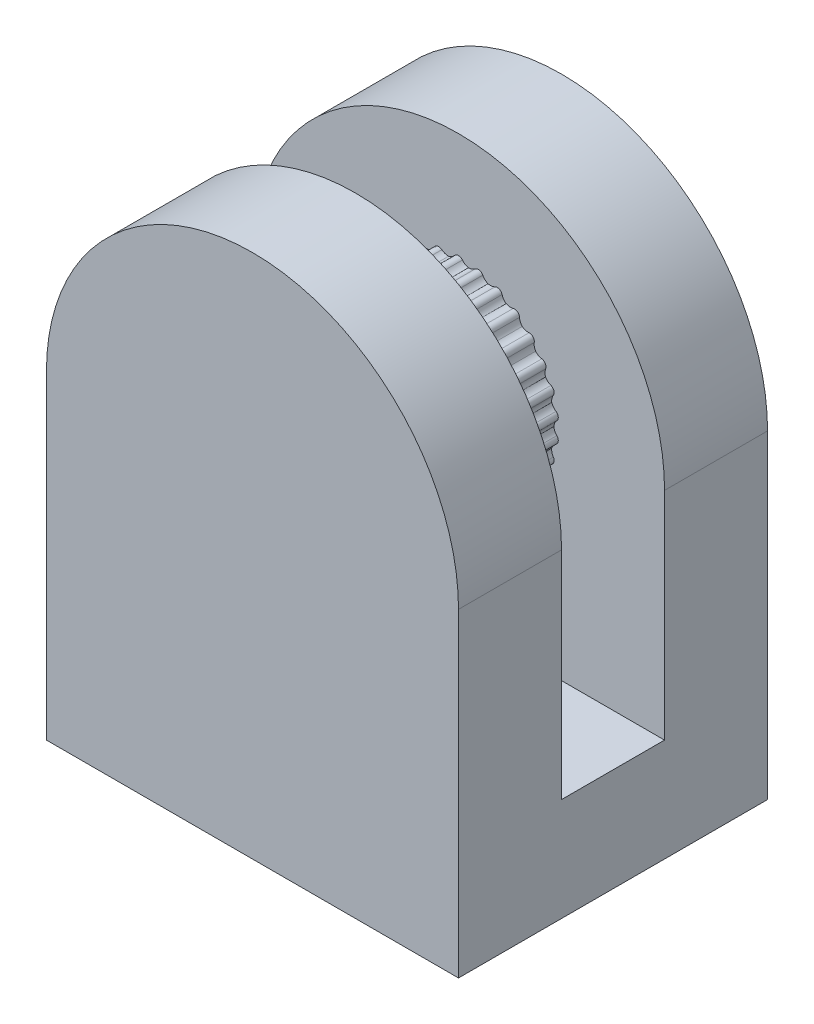
SolidWorks part; units mm, degrees
ref_plane "Front Plane" through (0, 0, 0) normal (0, 0, 1) x (1, 0, 0)
ref_plane "Top Plane" through (0, 0, 0) normal (0, 1, 0) x (1, 0, 0)
ref_plane "Right Plane" through (0, 0, 0) normal (1, 0, 0) x (0, 0, -1)
sketch "Sketch1" plane through (0, 0, 0) normal (0, 0, 1) x (1, 0, 0)
  circle A0 centre (0, 0) radius 20
  arc A1 (0.3787, 9.556) -> (-0.3787, 9.556) centre (0, 9.25) ccw
  arc A2 (2.3572, 9.2685) -> (1.6164, 9.4259) centre (1.9232, 9.0479) ccw
  arc A3 (4.2327, 8.5758) -> (3.5409, 8.8839) centre (3.7623, 8.4503) ccw
  arc A4 (5.9232, 7.5084) -> (5.3105, 7.9535) centre (5.437, 7.4834) ccw
  arc A5 (7.3549, 6.1128) -> (6.8481, 6.6756) centre (6.8741, 6.1895) ccw
  arc A6 (8.4651, 4.4501) -> (8.0864, 5.1059) centre (8.0107, 4.625) ccw
  arc A7 (9.2053, 2.5929) -> (8.9713, 3.3131) centre (8.7973, 2.8584) ccw
  arc A8 (9.5432, 0.6223) -> (9.4641, 1.3755) centre (9.1993, 0.9669) ccw
  arc A9 (9.4641, -1.3755) -> (9.5432, -0.6223) centre (9.1993, -0.9669) ccw
  arc A10 (8.9713, -3.3131) -> (9.2053, -2.5929) centre (8.7973, -2.8584) ccw
  arc A11 (8.0864, -5.1059) -> (8.4651, -4.4501) centre (8.0107, -4.625) ccw
  arc A12 (6.8481, -6.6756) -> (7.3549, -6.1128) centre (6.8741, -6.1895) ccw
  arc A13 (5.3105, -7.9535) -> (5.9232, -7.5084) centre (5.437, -7.4834) ccw
  arc A14 (3.5409, -8.8839) -> (4.2327, -8.5758) centre (3.7623, -8.4503) ccw
  arc A15 (1.6164, -9.4259) -> (2.3572, -9.2685) centre (1.9232, -9.0479) ccw
  arc A16 (-0.3787, -9.556) -> (0.3787, -9.556) centre (0, -9.25) ccw
  arc A17 (-2.3572, -9.2685) -> (-1.6164, -9.4259) centre (-1.9232, -9.0479) ccw
  arc A18 (-4.2327, -8.5758) -> (-3.5409, -8.8839) centre (-3.7623, -8.4503) ccw
  arc A19 (-5.9232, -7.5084) -> (-5.3105, -7.9535) centre (-5.437, -7.4834) ccw
  arc A20 (-7.3549, -6.1128) -> (-6.8481, -6.6756) centre (-6.8741, -6.1895) ccw
  arc A21 (-8.4651, -4.4501) -> (-8.0864, -5.1059) centre (-8.0107, -4.625) ccw
  arc A22 (-9.2053, -2.5929) -> (-8.9713, -3.3131) centre (-8.7973, -2.8584) ccw
  arc A23 (-9.5432, -0.6223) -> (-9.4641, -1.3755) centre (-9.1993, -0.9669) ccw
  arc A24 (-9.4641, 1.3755) -> (-9.5432, 0.6223) centre (-9.1993, 0.9669) ccw
  arc A25 (-8.9713, 3.3131) -> (-9.2053, 2.5929) centre (-8.7973, 2.8584) ccw
  arc A26 (-8.0864, 5.1059) -> (-8.4651, 4.4501) centre (-8.0107, 4.625) ccw
  arc A27 (-6.8481, 6.6756) -> (-7.3549, 6.1128) centre (-6.8741, 6.1895) ccw
  arc A28 (-5.3105, 7.9535) -> (-5.9232, 7.5084) centre (-5.437, 7.4834) ccw
  arc A29 (-3.5409, 8.8839) -> (-4.2327, 8.5758) centre (-3.7623, 8.4503) ccw
  arc A30 (-1.6164, 9.4259) -> (-2.3572, 9.2685) centre (-1.9232, 9.0479) ccw
  arc A31 (-0.3787, 9.556) -> (-0.9672, 9.2026) centre (-1.1564, 10.1846) cw
  arc A32 (0.9672, 9.2026) -> (0.3787, 9.556) centre (1.1564, 10.1846) cw
  arc A33 (1.6164, 9.4259) -> (0.9672, 9.2026) centre (0.9863, 10.2024) cw
  arc A34 (2.8594, 8.8004) -> (2.3572, 9.2685) centre (3.2486, 9.7216) cw
  arc A35 (3.5409, 8.8839) -> (2.8594, 8.8004) centre (3.086, 9.7744) cw
  arc A36 (4.6267, 8.0136) -> (4.2327, 8.5758) centre (5.1989, 8.8337) cw
  arc A37 (5.3105, 7.9535) -> (4.6267, 8.0136) centre (5.0508, 8.9192) cw
  arc A38 (6.1917, 6.8765) -> (5.9232, 7.5084) centre (6.9219, 7.5598) cw
  arc A39 (6.8481, 6.6756) -> (6.1917, 6.8765) centre (6.7948, 7.6742) cw
  arc A40 (7.4861, 5.439) -> (7.3549, 6.1128) centre (8.3424, 5.9554) cw
  arc A41 (8.0864, 5.1059) -> (7.4861, 5.439) centre (8.2419, 6.0938) cw
  arc A42 (8.4533, 3.7637) -> (8.4651, 4.4501) centre (9.3983, 4.0908) cw
  arc A43 (8.9713, 3.3131) -> (8.4533, 3.7637) centre (9.3287, 4.247) cw
  arc A44 (9.0511, 1.9239) -> (9.2053, 2.5929) centre (10.0434, 2.0474) cw
  arc A45 (9.4641, 1.3755) -> (9.0511, 1.9239) centre (10.0079, 2.2147) cw
  arc A46 (9.2533, 0) -> (9.5432, 0.6223) centre (10.2496, -0.0855) cw
  arc A47 (9.5432, -0.6223) -> (9.2533, 0) centre (10.2496, 0.0855) cw
  arc A48 (9.0511, -1.9239) -> (9.4641, -1.3755) centre (10.0079, -2.2147) cw
  arc A49 (9.2053, -2.5929) -> (9.0511, -1.9239) centre (10.0434, -2.0474) cw
  arc A50 (8.4533, -3.7637) -> (8.9713, -3.3131) centre (9.3287, -4.247) cw
  arc A51 (8.4651, -4.4501) -> (8.4533, -3.7637) centre (9.3983, -4.0908) cw
  arc A52 (7.4861, -5.439) -> (8.0864, -5.1059) centre (8.2419, -6.0938) cw
  arc A53 (7.3549, -6.1128) -> (7.4861, -5.439) centre (8.3424, -5.9554) cw
  arc A54 (6.1917, -6.8765) -> (6.8481, -6.6756) centre (6.7948, -7.6742) cw
  arc A55 (5.9232, -7.5084) -> (6.1917, -6.8765) centre (6.9219, -7.5598) cw
  arc A56 (4.6267, -8.0136) -> (5.3105, -7.9535) centre (5.0508, -8.9192) cw
  arc A57 (4.2327, -8.5758) -> (4.6267, -8.0136) centre (5.1989, -8.8337) cw
  arc A58 (2.8594, -8.8004) -> (3.5409, -8.8839) centre (3.086, -9.7744) cw
  arc A59 (2.3572, -9.2685) -> (2.8594, -8.8004) centre (3.2486, -9.7216) cw
  arc A60 (0.9672, -9.2026) -> (1.6164, -9.4259) centre (0.9863, -10.2024) cw
  arc A61 (0.3787, -9.556) -> (0.9672, -9.2026) centre (1.1564, -10.1846) cw
  arc A62 (-0.9672, -9.2026) -> (-0.3787, -9.556) centre (-1.1564, -10.1846) cw
  arc A63 (-1.6164, -9.4259) -> (-0.9672, -9.2026) centre (-0.9863, -10.2024) cw
  arc A64 (-2.8594, -8.8004) -> (-2.3572, -9.2685) centre (-3.2486, -9.7216) cw
  arc A65 (-3.5409, -8.8839) -> (-2.8594, -8.8004) centre (-3.086, -9.7744) cw
  arc A66 (-4.6267, -8.0136) -> (-4.2327, -8.5758) centre (-5.1989, -8.8337) cw
  arc A67 (-5.3105, -7.9535) -> (-4.6267, -8.0136) centre (-5.0508, -8.9192) cw
  arc A68 (-6.1917, -6.8765) -> (-5.9232, -7.5084) centre (-6.9219, -7.5598) cw
  arc A69 (-6.8481, -6.6756) -> (-6.1917, -6.8765) centre (-6.7948, -7.6742) cw
  arc A70 (-7.4861, -5.439) -> (-7.3549, -6.1128) centre (-8.3424, -5.9554) cw
  arc A71 (-8.0864, -5.1059) -> (-7.4861, -5.439) centre (-8.2419, -6.0938) cw
  arc A72 (-8.4533, -3.7637) -> (-8.4651, -4.4501) centre (-9.3983, -4.0908) cw
  arc A73 (-8.9713, -3.3131) -> (-8.4533, -3.7637) centre (-9.3287, -4.247) cw
  arc A74 (-9.0511, -1.9239) -> (-9.2053, -2.5929) centre (-10.0434, -2.0474) cw
  arc A75 (-9.4641, -1.3755) -> (-9.0511, -1.9239) centre (-10.0079, -2.2147) cw
  arc A76 (-9.2533, 0) -> (-9.5432, -0.6223) centre (-10.2496, 0.0855) cw
  arc A77 (-9.5432, 0.6223) -> (-9.2533, 0) centre (-10.2496, -0.0855) cw
  arc A78 (-9.0511, 1.9239) -> (-9.4641, 1.3755) centre (-10.0079, 2.2147) cw
  arc A79 (-9.2053, 2.5929) -> (-9.0511, 1.9239) centre (-10.0434, 2.0474) cw
  arc A80 (-8.4533, 3.7637) -> (-8.9713, 3.3131) centre (-9.3287, 4.247) cw
  arc A81 (-8.4651, 4.4501) -> (-8.4533, 3.7637) centre (-9.3983, 4.0908) cw
  arc A82 (-7.4861, 5.439) -> (-8.0864, 5.1059) centre (-8.2419, 6.0938) cw
  arc A83 (-7.3549, 6.1128) -> (-7.4861, 5.439) centre (-8.3424, 5.9554) cw
  arc A84 (-6.1917, 6.8765) -> (-6.8481, 6.6756) centre (-6.7948, 7.6742) cw
  arc A85 (-5.9232, 7.5084) -> (-6.1917, 6.8765) centre (-6.9219, 7.5598) cw
  arc A86 (-4.6267, 8.0136) -> (-5.3105, 7.9535) centre (-5.0508, 8.9192) cw
  arc A87 (-4.2327, 8.5758) -> (-4.6267, 8.0136) centre (-5.1989, 8.8337) cw
  arc A88 (-2.8594, 8.8004) -> (-3.5409, 8.8839) centre (-3.086, 9.7744) cw
  arc A89 (-2.3572, 9.2685) -> (-2.8594, 8.8004) centre (-3.2486, 9.7216) cw
  arc A90 (-0.9672, 9.2026) -> (-1.6164, 9.4259) centre (-0.9863, 10.2024) cw
  point P64 (0, 0)
  point P66 (-0.4867, 9.2372)
  point P68 (0.4867, 9.2372)
  point P185 (0, 0)
  point P186 (0, 0)
  point P187 (0, 0)
  dimension "D1" = 40
  dimension "D2" = 1
  dimension "D3" = 1
extrude "Boss-Extrude1" add sketch "Sketch1" along normal blind 10 contours A1 A31 A90 A30 A89 A88 A29 A87 A86 A28 A85 A84 A27 A83 A82 A26 A81 A80 A25 A79 A78 A24 A77 A76 A23 A75 A74 A22 A73 A72 A21 A71 A70 A20 A69 A68 A19 A67 A66 A18 A65 A64 A17 A63 A62 A16 A61 A60 A15 A59 A58 A14 A57 A56 A13 A55 A54 A12 A53 A52 A11 A51 A50 A10 A49 A48 A9 A47 A46 A8 A45 A44 A7 A43 A42 A6 A41 A40 A5 A39 A38 A4 A37 A36 A3 A35 A34 A2 A33 A32
sketch "Sketch2" plane through (0, 0, 0) normal (0, 0, -1) x (-1, 0, 0)
  line L2 (-20, 0) -> (-20, -30.9919)
  line L3 (-20, -30.9919) -> (20, -30.9919)
  line L4 (20, 0) -> (20, -30.9919)
  arc A0 (20, 0) -> (-20, 0) centre (0, 0) ccw
extrude "Boss-Extrude2" add sketch "Sketch2" along normal blind 10
ref_plane "Plane2" through (0, 0, 5) normal (0, 0, 1) x (1, 0, 0)
mirror "Mirror2" about plane through (0, 0, 5) normal (0, 0, 1) of "Boss-Extrude2"
sketch "Sketch3" plane through (0, 0, 10) normal (0, 0, -1) x (-1, 0, 0)
  line L0 (20, -30.9919) -> (20, 0) construction
  line L1 (-20, -30.9919) -> (20, -30.9919)
  line L2 (-20, -30.9919) -> (-20, -20.9919)
  line L3 (-20, -20.9919) -> (20, -20.9919)
  line L4 (20, -30.9919) -> (20, -20.9919)
  dimension "D1" = 10
extrude "Boss-Extrude3" add sketch "Sketch3" along normal up to surface (10 mm away) up to face at (0, -10.496, 0)
